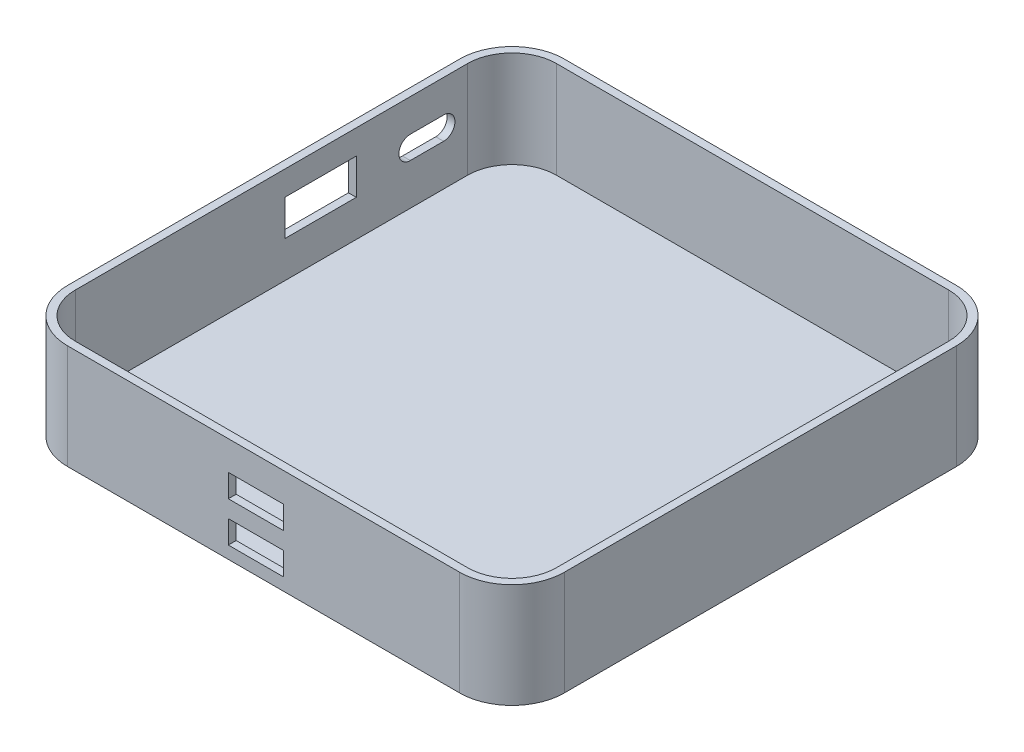
SolidWorks part; units mm, degrees
ref_plane "Front Plane" through (0, 0, 0) normal (0, 0, 1) x (1, 0, 0)
ref_plane "Top Plane" through (0, 0, 0) normal (0, 1, 0) x (1, 0, 0)
ref_plane "Right Plane" through (0, 0, 0) normal (1, 0, 0) x (0, 0, -1)
sketch "Sketch1" plane through (0, 0, 0) normal (0, 1, 0) x (1, 0, 0)
  line L1 (-47.5, 47.5) -> (47.5, 47.5)
  line L2 (-47.5, 47.5) -> (-47.5, -47.5)
  line L3 (-47.5, -47.5) -> (47.5, -47.5)
  line L4 (47.5, 47.5) -> (47.5, -47.5)
  line L5 (-47.5, 47.5) -> (47.5, -47.5) construction
  line L6 (-47.5, -47.5) -> (47.5, 47.5) construction
  point P0 (0, 0)
  dimension "D1" = 95
  dimension "D2" = 95
extrude "Boss-Extrude1" add sketch "Sketch1" along normal blind 20
fillet "Fillet1" radius 10 4 edges at (-47.5, 10, -47.5) (-47.5, 10, 47.5) (47.5, 10, -47.5) (47.5, 10, 47.5)
sketch "Sketch4" plane through (0, 20, 0) normal (0, 1, 0) x (1, 0, 0)
  line L9 (37.5, 46) -> (-37.5, 46)
  line L10 (-46, 37.5) -> (-46, -37.5)
  line L11 (-37.5, -46) -> (37.5, -46)
  line L12 (46, -37.5) -> (46, 37.5)
  line L13 (37.5, 46) -> (-37.5, 46)
  line L14 (-46, 37.5) -> (-46, -37.5)
  line L15 (-37.5, -46) -> (37.5, -46)
  line L16 (46, -37.5) -> (46, 37.5)
  arc A10 (-37.5, 46) -> (-46, 37.5) centre (-37.5, 37.5) ccw
  arc A11 (-46, -37.5) -> (-37.5, -46) centre (-37.5, -37.5) ccw
  arc A12 (37.5, -46) -> (46, -37.5) centre (37.5, -37.5) ccw
  arc A13 (46, 37.5) -> (37.5, 46) centre (37.5, 37.5) ccw
  arc A14 (-37.5, 46) -> (-46, 37.5) centre (-37.5, 37.5) ccw
  arc A15 (-46, -37.5) -> (-37.5, -46) centre (-37.5, -37.5) ccw
  arc A16 (37.5, -46) -> (46, -37.5) centre (37.5, -37.5) ccw
  arc A17 (46, 37.5) -> (37.5, 46) centre (37.5, 37.5) ccw
  dimension "D1" = 1.5
extrude "Cut-Extrude5" cut sketch "Sketch4" against normal blind 18.5
sketch "Sketch5" plane through (-47.5, 0, 0) normal (-1, 0, 0) x (0, 0, 1)
  line L0 (-32.9171, 11.5887) -> (-26.5459, 11.5887) construction
  line L1 (-32.9171, 13.7636) -> (-26.5459, 13.7636)
  line L2 (-32.9171, 9.4138) -> (-26.5459, 9.4138)
  arc A0 (-32.9171, 13.7636) -> (-32.9171, 9.4138) centre (-32.9171, 11.5887) ccw
  arc A1 (-26.5459, 9.4138) -> (-26.5459, 13.7636) centre (-26.5459, 11.5887) ccw
  point P2 (-29.7315, 11.5887)
extrude "Cut-Extrude6" cut sketch "Sketch5" against normal blind 10
sketch "Sketch6" plane through (-47.5, 0, 0) normal (-1, 0, 0) x (0, 0, 1)
  line L9 (-16.2201, 8.4817) -> (-2.5989, 8.4817)
  line L10 (-16.2201, 8.4817) -> (-16.2201, 15.317)
  line L11 (-16.2201, 15.317) -> (-2.5989, 15.317)
  line L12 (-2.5989, 8.4817) -> (-2.5989, 15.317)
  line L13 (-16.2201, 8.4817) -> (-2.5989, 15.317) construction
  line L14 (-16.2201, 15.317) -> (-2.5989, 8.4817) construction
  point P0 (-9.4095, 11.8994)
extrude "Cut-Extrude7" cut sketch "Sketch6" against normal blind 10
sketch "Sketch9" plane through (0, 0, 47.5) normal (0, 0, 1) x (1, 0, 0)
  line L5 (-6.7491, 6.7594) -> (3.8346, 6.7594)
  line L6 (-6.7491, 6.7594) -> (-6.7491, 2.38)
  line L7 (-6.7491, 2.38) -> (3.8346, 2.38)
  line L8 (3.8346, 6.7594) -> (3.8346, 2.38)
  line L9 (-6.7491, 6.7594) -> (3.8346, 2.38) construction
  line L10 (-6.7491, 2.38) -> (3.8346, 6.7594) construction
  line L11 (-6.7491, 10.044) -> (3.8346, 10.044)
  line L12 (-6.7491, 10.044) -> (-6.7491, 14.4235)
  line L13 (-6.7491, 14.4235) -> (3.8346, 14.4235)
  line L14 (3.8346, 10.044) -> (3.8346, 14.4235)
  line L15 (-6.7491, 10.044) -> (3.8346, 14.4235) construction
  line L16 (-6.7491, 14.4235) -> (3.8346, 10.044) construction
  point P0 (-1.4572, 4.5697)
  point P5 (-1.4572, 12.2337)
extrude "Cut-Extrude10" cut sketch "Sketch9" against normal blind 10
